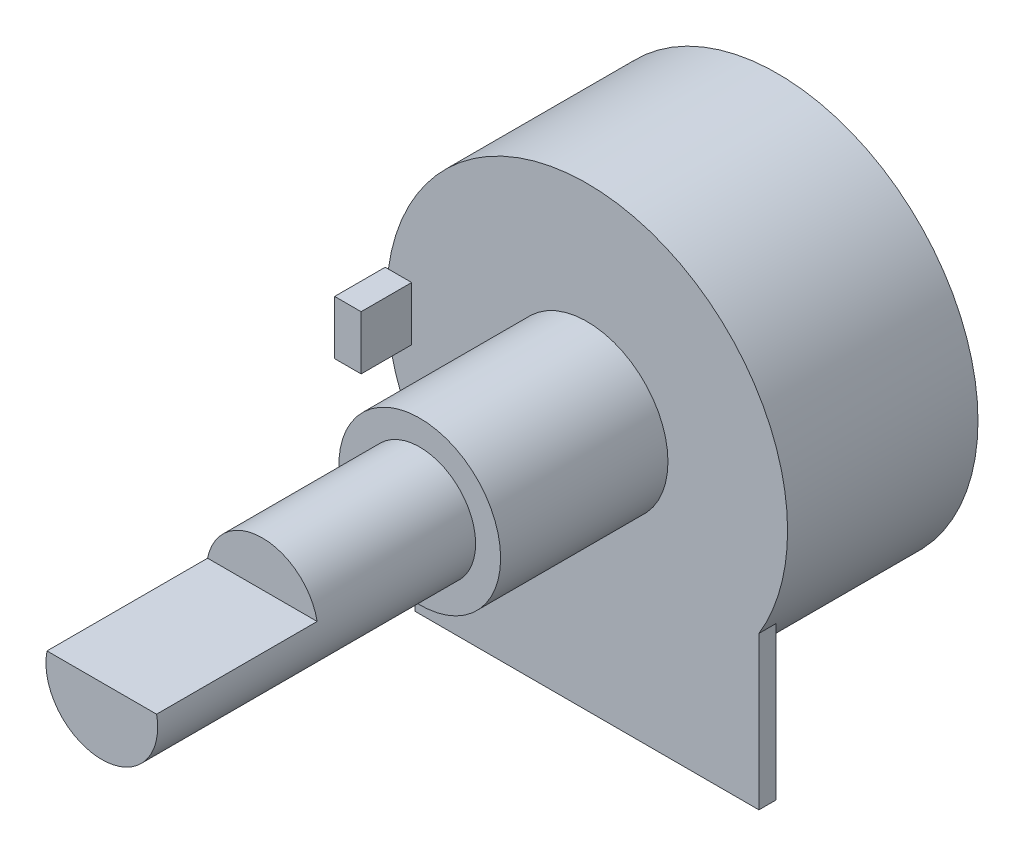
SolidWorks part; units mm, degrees
ref_plane "Alzado" through (0, 0, 0) normal (0, 0, 1) x (1, 0, 0)
ref_plane "Planta" through (0, 0, 0) normal (0, 1, 0) x (1, 0, 0)
ref_plane "Vista lateral" through (0, 0, 0) normal (1, 0, 0) x (0, 0, -1)
sketch "Croquis1" plane through (0, 0, 0) normal (1, 0, 0) x (0, 0, -1)
  line L24 (-1000, 0) -> (49000, 0) construction
  line L25 (0, 0) -> (11.3, 0)
  line L26 (11.3, 0) -> (11.3, 11.9)
  line L27 (11.3, 11.9) -> (0, 11.9)
  line L28 (0, 11.9) -> (0, 4.8)
  line L29 (0, 4.8) -> (-9.93, 4.8)
  line L30 (-9.93, 4.8) -> (-9.93, 3.315)
  line L31 (-9.93, 3.315) -> (-28.8, 3.315)
  line L32 (-28.8, 3.315) -> (-28.8, 0)
  line L33 (-28.8, 0) -> (0, 0)
  line L34 (-9.93, -3.315) -> (-28.8, -3.315) construction
  line L35 (-9.93, -4.8) -> (-9.93, -3.315) construction
  line L36 (0, -4.8) -> (-9.93, -4.8) construction
  line L37 (0, -11.9) -> (0, -4.8) construction
  line L38 (11.3, -11.9) -> (0, -11.9) construction
  dimension "D1" = 11.3
  dimension "D2" = 28.8
  dimension "D3" = 23.8
  dimension "D4" = 9.93
  dimension "D5" = 9.6
  dimension "D6" = 6.63
revolve "Revolución2" add sketch "Croquis1" angle 360 about L33
sketch "Croquis2" plane through (0, 0, 0) normal (0, 0, 1) x (1, 0, 0)
  line L0 (0, 0) -> (10.41, 0) construction
  line L1 (0, -1000) -> (0, 49000) construction
  line L2 (-11.98, -1.6) -> (-10.41, -1.6)
  line L3 (11.98, 1.6) -> (10.41, 1.6) construction
  line L4 (11.98, 1.6) -> (11.98, -1.6) construction
  line L5 (11.98, -1.6) -> (10.41, -1.6) construction
  line L6 (10.41, 1.6) -> (10.41, -1.6) construction
  line L7 (-10.41, 1.6) -> (-10.41, -1.6)
  line L8 (-11.98, 1.6) -> (-10.41, 1.6)
  line L9 (-11.98, 1.6) -> (-11.98, -1.6)
  dimension "D1" = 10.41
  dimension "D2" = 3.2
  dimension "D3" = 1.57
extrude "Saliente-Extruir1" add sketch "Croquis2" along normal blind 3
sketch "Croquis3" plane through (0, 0, 0) normal (0, 0, 1) x (1, 0, 0)
  line L0 (0, 0) -> (0, -15.2) construction
  line L1 (-10.2, -15.2) -> (10.2, -15.2)
  line L2 (-10.2, -15.2) -> (-10.2, -6.1294)
  line L3 (10.2, -15.2) -> (10.2, -6.1294)
  line L7 (-10.41, -1.6) -> (-11.7919, -1.6)
  line L8 (-11.7919, 1.6) -> (-10.41, 1.6)
  line L9 (-10.41, 1.6) -> (-10.41, -1.6)
  arc A0 (-11.7919, -1.6) -> (-11.7919, 1.6) centre (0, 0) ccw construction
  arc A2 (-11.7919, -1.6) -> (-11.7919, 1.6) centre (0, 0) ccw
  arc A3 (-10.2, -6.1294) -> (10.2, -6.1294) centre (0, 0) ccw
  point P5 (0, -15.2)
  dimension "D1" = 15.2
  dimension "D2" = 20.4
  dimension "D3" = 0
extrude "Saliente-Extruir2" add sketch "Croquis3" against normal blind 1
sketch "Croquis4" plane through (0, 0, 0) normal (1, 0, 0) x (0, 0, -1)
  line L0 (-28.8, -3.315) -> (-9.93, -3.315) construction
  line L1 (-28.8, 3.315) -> (-19.27, 3.315)
  line L2 (-28.8, 3.315) -> (-28.8, 0.645)
  line L3 (-28.8, 0.645) -> (-19.27, 0.645)
  line L4 (-19.27, 3.315) -> (-19.27, 0.645)
  dimension "D1" = 9.53
  dimension "D2" = 3.96
extrude "Cortar-Extruir1" cut sketch "Croquis4" against normal through all both and the other way through all
